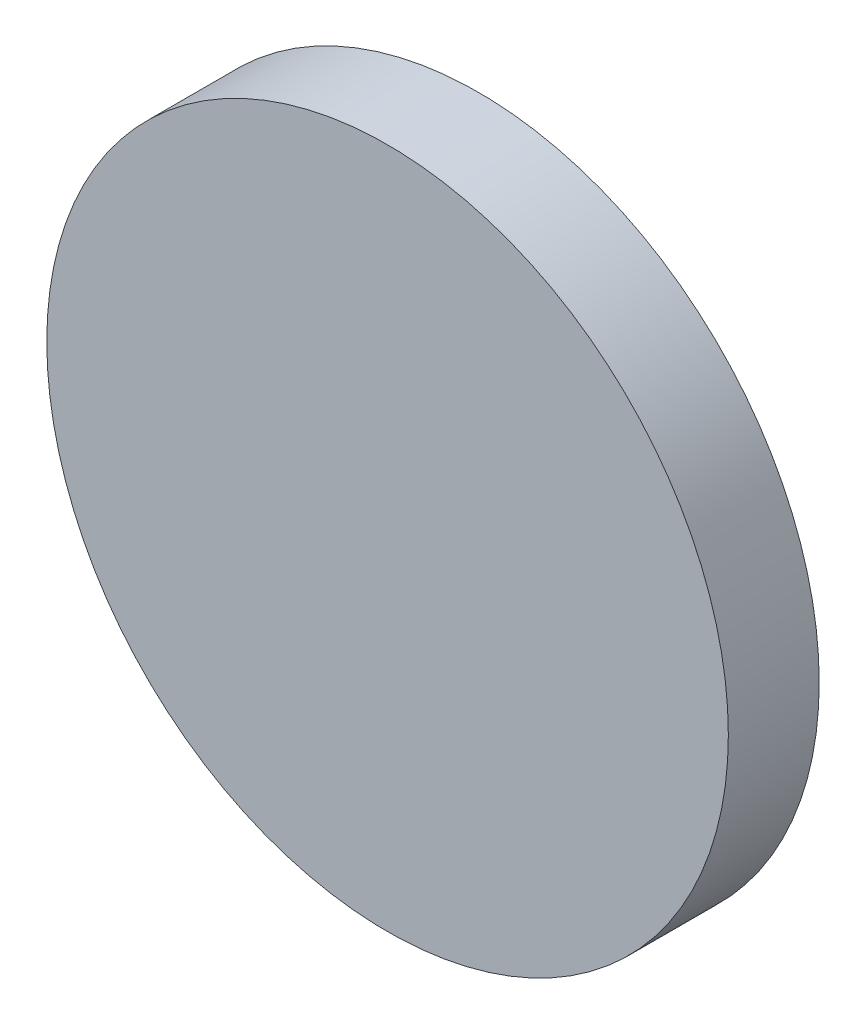
SolidWorks part; units mm, degrees
ref_plane "Alzado" through (0, 0, 0) normal (0, 0, 1) x (1, 0, 0)
ref_plane "Planta" through (0, 0, 0) normal (0, 1, 0) x (1, 0, 0)
ref_plane "Vista lateral" through (0, 0, 0) normal (1, 0, 0) x (0, 0, -1)
sketch "Croquis1" plane through (0, 0, 0) normal (0, 0, 1) x (1, 0, 0)
  circle A0 centre (0, 0) radius 7.5
  dimension "D1" = 15
extrude "Saliente-Extruir1" add sketch "Croquis1" along normal blind 2
sketch "Croquis2" plane through (0, 0, 0) normal (0, 0, -1) x (-1, 0, 0)
  circle A0 centre (0, 0) radius 5.015
  dimension "D1" = 10.03
extrude "Cortar-Extruir1" cut sketch "Croquis2" against normal blind 0.5
